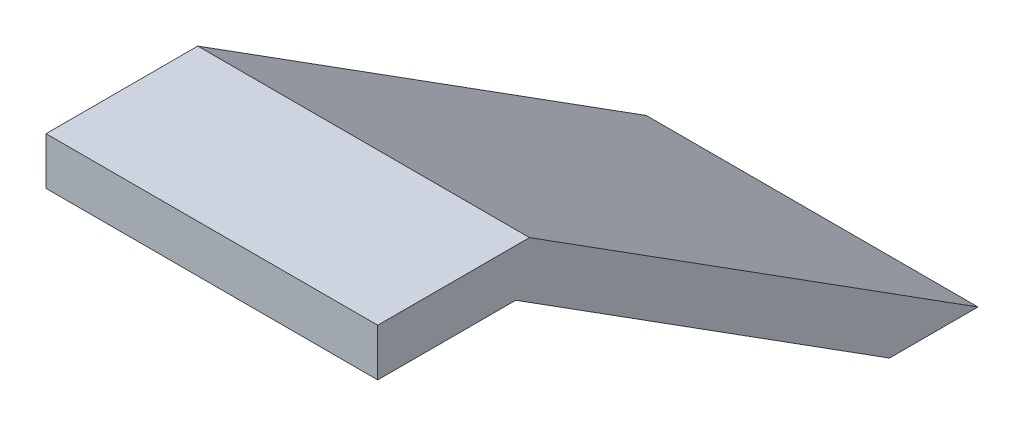
SolidWorks part; units mm, degrees
ref_plane "Alzado" through (0, 0, 0) normal (0, 0, 1) x (1, 0, 0)
ref_plane "Planta" through (0, 0, 0) normal (0, 1, 0) x (1, 0, 0)
ref_plane "Vista lateral" through (0, 0, 0) normal (1, 0, 0) x (0, 0, -1)
sketch "Croquis2" plane through (0, 0, 0) normal (1, 0, 0) x (0, 0, -1)
  line L1 (-41.2833, 1.4772) -> (1.7167, 1.4772)
  line L2 (-41.2833, 1.4772) -> (-41.2833, -28.5228)
  line L3 (-41.2833, -28.5228) -> (1.7167, -28.5228)
  line L4 (1.7167, 1.4772) -> (1.7167, -28.5228)
  dimension "D1" = 30
  dimension "D2" = 43
extrude "Saliente-Extruir1" add sketch "Croquis2" along normal blind 30
sketch "Croquis3" plane through (30, 0, 0) normal (1, 0, 0) x (0, 0, -1)
  line L0 (-41.2833, 1.4772) -> (-41.2833, -28.5228) construction
  line L1 (-38.2833, -44.0813) -> (4.2461, -44.0813)
  line L2 (-38.2833, -44.0813) -> (-38.2833, -18.5228)
  line L3 (-38.2833, -18.5228) -> (4.2461, -18.5228)
  line L4 (4.2461, -44.0813) -> (4.2461, -18.5228)
  line L5 (-41.2833, -28.5228) -> (1.7167, -28.5228) construction
  line L6 (-31.6751, 1.4772) -> (-3.2833, -16.5228)
  line L7 (1.7167, 1.4772) -> (-41.2833, 1.4772) construction
  line L8 (-3.2833, -16.5228) -> (1.7167, -16.5228)
  line L9 (1.7167, -28.5228) -> (1.7167, 1.4772) construction
  line L10 (1.7167, -16.5228) -> (1.7167, 1.4772)
  line L11 (1.7167, 1.4772) -> (-31.6751, 1.4772)
  dimension "D1" = 3
  dimension "D2" = 10
  dimension "D3" = 2
  dimension "D4" = 5
extrude "Cortar-Extruir1" cut sketch "Croquis3" against normal blind 30
sketch "Croquis4" plane through (30, 0, 0) normal (1, 0, 0) x (0, 0, -1)
  line L0 (-41.2833, -1.5228) -> (-32.5459, -1.5228)
  line L1 (-41.2833, 1.4772) -> (-41.2833, -28.5228) construction
  line L2 (-32.5459, -1.5228) -> (-8.8861, -16.5228)
  line L3 (-8.8861, -16.5228) -> (-41.2833, -16.5228)
  line L4 (-41.2833, -16.5228) -> (-41.2833, -1.5228)
  line L5 (-31.6751, 1.4772) -> (-41.2833, 1.4772) construction
  line L6 (1.7167, -18.5228) -> (-38.2833, -18.5228) construction
  line L7 (-31.6751, 1.4772) -> (-3.2833, -16.5228) construction
  dimension "D1" = 3
  dimension "D2" = 2
  dimension "D3" = 3
extrude "Cortar-Extruir2" cut sketch "Croquis4" against normal offset from surface (15 mm away) 7.5 from offset 7.5 up to face at (0, -15.5228, 23.8322) offset against normal yes
sketch "Croquis5" plane through (30, 0, 0) normal (1, 0, 0) x (0, 0, -1)
  line L1 (-3.2833, -16.5228) -> (-41.2833, -16.5228)
  line L8 (-38.2833, -28.5228) -> (-38.2833, -18.5228)
  line L9 (-38.2833, -18.5228) -> (1.7167, -18.5228)
  line L10 (1.7167, -18.5228) -> (1.7167, -16.5228)
  line L11 (1.7167, -16.5228) -> (-3.2833, -16.5228)
  line L12 (-3.2833, -16.5228) -> (-31.6751, 1.4772)
  line L13 (-31.6751, 1.4772) -> (-41.2833, 1.4772)
  line L14 (-41.2833, 1.4772) -> (-41.2833, -28.5228)
  line L15 (-41.2833, -28.5228) -> (-38.2833, -28.5228)
  line L20 (-3.2833, -16.5228) -> (-31.6751, 1.4772)
  line L21 (-31.6751, 1.4772) -> (-41.2833, 1.4772)
  line L22 (-41.2833, 1.4772) -> (-41.2833, -16.5228)
  dimension "D1" = 0
extrude "Cortar-Extruir4" cut sketch "Croquis5" against normal blind 4.5
sketch "Croquis6" plane through (0, 0, 0) normal (-1, 0, 0) x (0, 0, 1)
  line L0 (3.2833, -16.5228) -> (41.2833, -16.5228)
  line L8 (-1.7167, -18.5228) -> (38.2833, -18.5228)
  line L9 (38.2833, -18.5228) -> (38.2833, -28.5228)
  line L10 (38.2833, -28.5228) -> (41.2833, -28.5228)
  line L11 (41.2833, -28.5228) -> (41.2833, 1.4772)
  line L12 (41.2833, 1.4772) -> (31.6751, 1.4772)
  line L13 (31.6751, 1.4772) -> (3.2833, -16.5228)
  line L14 (3.2833, -16.5228) -> (-1.7167, -16.5228)
  line L15 (-1.7167, -16.5228) -> (-1.7167, -18.5228)
  line L19 (41.2833, -16.5228) -> (41.2833, 1.4772)
  line L20 (41.2833, 1.4772) -> (31.6751, 1.4772)
  line L21 (31.6751, 1.4772) -> (3.2833, -16.5228)
  dimension "D1" = 0
extrude "Cortar-Extruir5" cut sketch "Croquis6" against normal blind 4.5
fillet "Redondeo1" radius 3 2 edges at (30, -17.5228, -1.7167) (0, -17.5228, -1.7167)
sketch "Croquis8" plane through (0, -16.5228, 0) normal (0, 1, 0) x (1, 0, 0)
  line L4 (7.5, -8.8861) -> (7.5, -41.2833)
  line L5 (7.5, -41.2833) -> (22.5, -41.2833)
  line L6 (22.5, -41.2833) -> (22.5, -8.8861)
  line L7 (22.5, -8.8861) -> (7.5, -8.8861)
  line L8 (7.5, -8.8861) -> (7.5, -41.2833)
  line L9 (7.5, -41.2833) -> (22.5, -41.2833)
  line L10 (22.5, -41.2833) -> (22.5, -8.8861)
  line L11 (22.5, -8.8861) -> (7.5, -8.8861)
  dimension "D1" = 0
extrude "Cortar-Extruir6" cut sketch "Croquis8" against normal blind 4.5
sketch "Croquis9" plane through (0, -18.5228, 0) normal (0, -1, 0) x (1, 0, 0)
  line L1 (77.7572, 22.6846) -> (-42.526, 22.6846)
  line L2 (77.7572, 22.6846) -> (77.7572, 101.4947)
  line L3 (77.7572, 101.4947) -> (-42.526, 101.4947)
  line L4 (-42.526, 22.6846) -> (-42.526, 101.4947)
extrude "Cortar-Extruir7" cut sketch "Croquis9" along normal blind 22.5
sketch "Croquis10" plane through (25.5, 0, 0) normal (1, 0, 0) x (0, 0, -1)
  line L0 (-41.2833, -1.5228) -> (-32.5459, -1.5228)
  line L1 (-32.5459, -1.5228) -> (-8.8861, -16.5228)
  line L2 (-8.8861, -16.5228) -> (1.7167, -16.5228)
  line L3 (1.7167, -16.5228) -> (18.1089, -28.4576)
  line L4 (18.1089, -28.4576) -> (-61.7999, -25.2418)
  line L5 (-61.7999, -25.2418) -> (-41.2833, -1.5228)
  point P6 (-61.7999, -25.2418)
extrude "Cortar-Extruir9" cut sketch "Croquis10" against normal blind 29.5 and the other way blind 22.5
